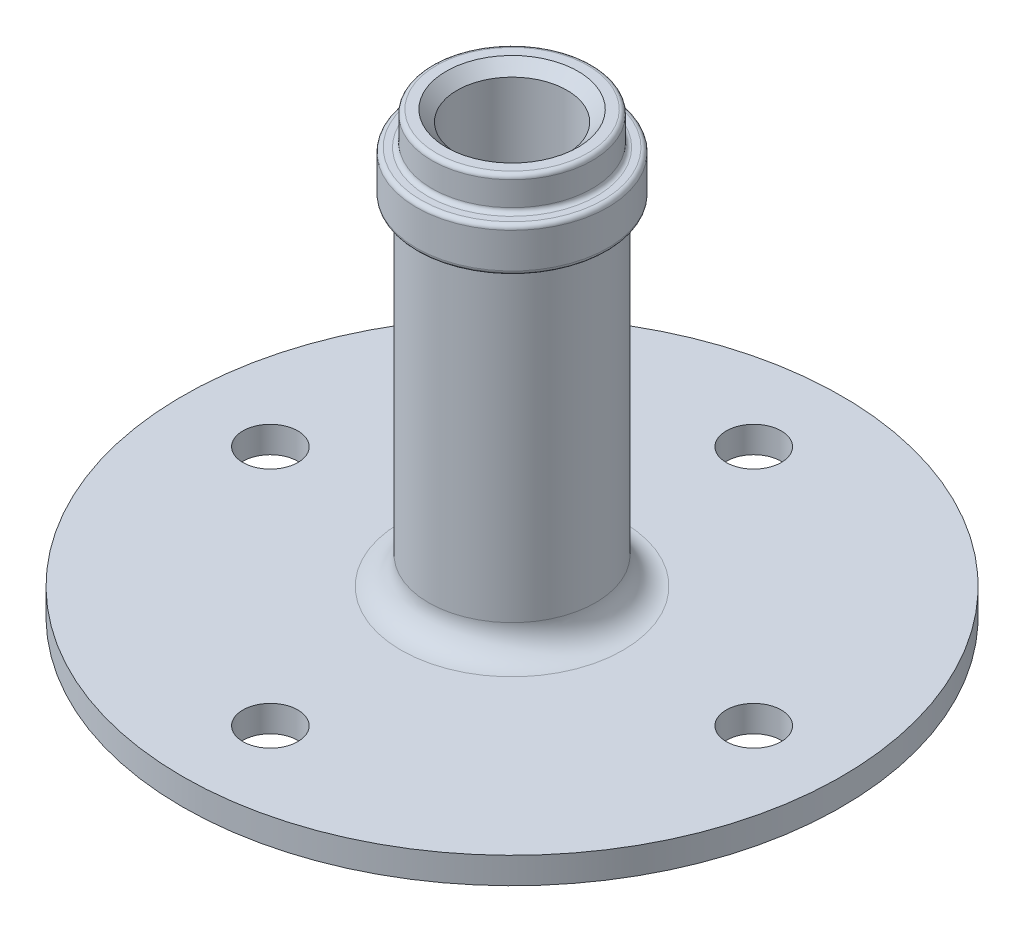
SolidWorks part; units mm, degrees
material "6061-T6 (SS)"
ref_plane "Front Plane" through (0, 0, 0) normal (0, 0, 1) x (1, 0, 0)
ref_plane "Top Plane" through (0, 0, 0) normal (0, 1, 0) x (1, 0, 0)
ref_plane "Right Plane" through (0, 0, 0) normal (1, 0, 0) x (0, 0, -1)
sketch "Sketch1" plane through (0, 0, 0) normal (0, 0, 1) x (1, 0, 0)
  line L0 (4.6355, 25.146) -> (4.6355, 23.749)
  line L1 (4.8895, 23.495) -> (5.2705, 23.495)
  line L2 (5.5245, 23.241) -> (5.5245, 21.209)
  line L3 (3.175, 0) -> (3.175, 24.765)
  line L4 (3.81, 25.4) -> (4.3815, 25.4)
  line L5 (0, 26.6065) -> (0, -0.762) construction
  line L6 (3.175, 0) -> (19.05, 0)
  line L7 (4.826, 20.701) -> (4.826, 3.1115)
  line L8 (6.4135, 1.524) -> (19.05, 1.524)
  line L9 (19.05, 1.524) -> (19.05, 0)
  line L10 (5.2705, 20.955) -> (5.08, 20.955)
  line L11 (3.175, 24.765) -> (3.81, 25.4)
  arc A0 (4.826, 3.1115) -> (6.4135, 1.524) centre (6.4135, 3.1115) ccw
  arc A1 (4.3815, 25.4) -> (4.6355, 25.146) centre (4.3815, 25.146) cw
  arc A2 (4.6355, 23.749) -> (4.8895, 23.495) centre (4.8895, 23.749) ccw
  arc A3 (5.2705, 23.495) -> (5.5245, 23.241) centre (5.2705, 23.241) cw
  arc A4 (5.5245, 21.209) -> (5.2705, 20.955) centre (5.2705, 21.209) cw
  arc A5 (4.826, 20.701) -> (5.08, 20.955) centre (5.08, 20.701) cw
  point P6 (3.175, 25.4)
  point P16 (4.6355, 25.4)
  point P20 (4.6355, 23.495)
  point P27 (4.826, 20.955)
  dimension "D7" = 1.5875
  dimension "D6" = 0.254
  dimension "D1" = 1.524
  dimension "D2" = 15.875
  dimension "D3" = 6.35
  dimension "D4" = 9.652
  dimension "D5" = 11.049
  dimension "D8" = 25.4
  dimension "D9" = 9.271
  dimension "D10" = 1.905
  dimension "D12" = 2.54
revolve "Revolve1" add sketch "Sketch1" angle 360 about L5
sketch "Sketch2" plane through (0, 1.524, 0) normal (0, 1, 0) x (1, 0, 0)
  circle A0 centre (0, 0) radius 13.97 construction
  circle A1 centre (0, 13.97) radius 1.5875
  circle A2 centre (13.97, 0) radius 1.5875
  circle A3 centre (0, -13.97) radius 1.5875
  circle A4 centre (-13.97, 0) radius 1.5875
  circle A6 centre (0, 0) radius 19.05 construction
  dimension "D1" = 3.175
  dimension "D3" = 5.08
  dimension "D2" = 4
extrude "Cut-Extrude1" cut sketch "Sketch2" against normal through all
